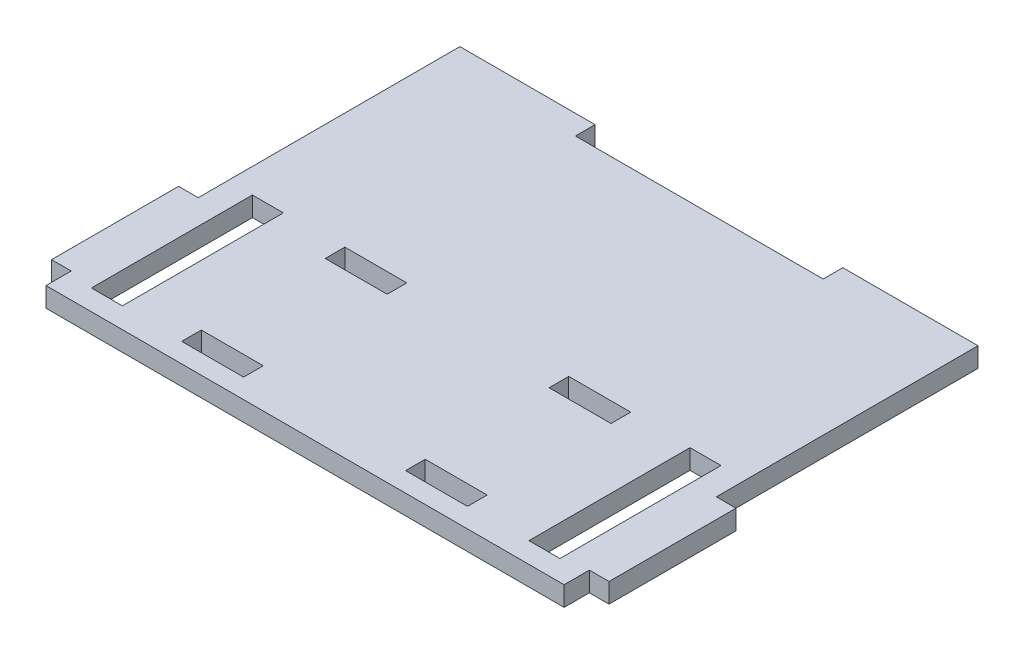
SolidWorks part; units mm, degrees
ref_plane "Front Plane" through (0, 0, 0) normal (0, 0, 1) x (1, 0, 0)
ref_plane "Top Plane" through (0, 0, 0) normal (0, 1, 0) x (1, 0, 0)
ref_plane "Right Plane" through (0, 0, 0) normal (1, 0, 0) x (0, 0, -1)
sketch "Sketch1" plane through (0, 0, 0) normal (0, 1, 0) x (1, 0, 0)
  line L0 (-41.825, 31.825) -> (41.825, 31.825)
  line L1 (-45, -35) -> (45, -35)
  line L2 (-45, -35) -> (-45, 35)
  line L3 (-45, 35) -> (45, 35)
  line L4 (45, -35) -> (45, 35)
  line L5 (-45, -35) -> (45, 35) construction
  line L6 (-45, 35) -> (45, -35) construction
  line L7 (41.825, -35) -> (41.825, 35)
  line L8 (-41.825, -31.825) -> (41.825, -31.825)
  line L9 (-41.825, -35) -> (-41.825, 35)
  line L10 (-41.825, -31.825) -> (-41.825, 31.825) construction
  line L11 (-20, 38.175) -> (20, 38.175)
  line L12 (-20, 38.175) -> (-20, 31.825)
  line L13 (-20, 31.825) -> (20, 31.825)
  line L14 (20, 38.175) -> (20, 31.825)
  line L15 (-20, 38.175) -> (20, 31.825) construction
  line L16 (-20, 31.825) -> (20, 38.175) construction
  line L17 (-20, -38.175) -> (20, -38.175)
  line L18 (-20, -38.175) -> (-20, -31.825)
  line L19 (-20, -31.825) -> (20, -31.825)
  line L20 (20, -38.175) -> (20, -31.825)
  line L21 (-20, -38.175) -> (20, -31.825) construction
  line L22 (-20, -31.825) -> (20, -38.175) construction
  line L23 (-48.175, -27.75) -> (-41.825, -27.75)
  line L24 (-48.175, -27.75) -> (-48.175, -7.25)
  line L25 (-48.175, -7.25) -> (-41.825, -7.25)
  line L26 (-41.825, -27.75) -> (-41.825, -7.25)
  line L27 (-48.175, -27.75) -> (-41.825, -7.25) construction
  line L28 (-48.175, -7.25) -> (-41.825, -27.75) construction
  line L29 (0, 0) -> (0, -35) construction
  line L30 (48.175, -7.25) -> (41.825, -27.75) construction
  line L31 (48.175, -27.75) -> (41.825, -7.25) construction
  line L32 (41.825, -27.75) -> (41.825, -7.25)
  line L33 (48.175, -7.25) -> (41.825, -7.25)
  line L34 (48.175, -27.75) -> (48.175, -7.25)
  line L35 (41.825, -31.825) -> (41.825, 31.825) construction
  line L36 (48.175, -27.75) -> (41.825, -27.75)
  point P0 (0, 0)
  point P10 (0, 35)
  point P15 (0, -35)
  point P20 (-45, 0)
  point P35 (45, -17.5)
  point P36 (-45, -17.5)
  dimension "D1" = 70
  dimension "D2" = 90
  dimension "D4" = 40
  dimension "D5" = 20.5
  dimension "D6" = 17.5
  dimension "D3" = 3.175
extrude "Boss-Extrude1" add sketch "Sketch1" along normal blind 3.175 contours L9 L8 L7 L0 | L3 L14 L0 L7 | L12 L3 L9 L0 | L25 L2 L23 L9 | L36 L4 L33 L7
sketch "Sketch2" plane through (0, 3.175, 0) normal (0, 1, 0) x (1, 0, 0)
  line L1 (-37.825, -28.5) -> (-32.825, -28.5)
  line L2 (-37.825, -28.5) -> (-37.825, -2.5)
  line L3 (-37.825, -2.5) -> (-32.825, -2.5)
  line L4 (-32.825, -28.5) -> (-32.825, -2.5)
  line L5 (-37.825, -28.5) -> (-32.825, -2.5) construction
  line L6 (-37.825, -2.5) -> (-32.825, -28.5) construction
  line L7 (-41.825, -31.825) -> (-41.825, -27.75) construction
  line L8 (0, -31.825) -> (0, 31.825) construction
  line L9 (-41.825, -31.825) -> (41.825, -31.825) construction
  line L10 (-20, 31.825) -> (20, 31.825) construction
  line L11 (37.825, -2.5) -> (32.825, -28.5) construction
  line L12 (37.825, -28.5) -> (32.825, -2.5) construction
  line L13 (32.825, -28.5) -> (32.825, -2.5)
  line L14 (37.825, -2.5) -> (32.825, -2.5)
  line L15 (37.825, -28.5) -> (37.825, -2.5)
  line L16 (37.825, -28.5) -> (32.825, -28.5)
  line L17 (-35.325, -15.5) -> (35.325, -15.5) construction
  line L18 (-18.075, -15.5) -> (-18.075, -3.9125) construction
  line L19 (23.075, -2.325) -> (13.075, -5.5) construction
  line L20 (-23.075, -5.5) -> (-13.075, -5.5)
  line L21 (-23.075, -5.5) -> (-23.075, -2.325)
  line L22 (-23.075, -2.325) -> (-13.075, -2.325)
  line L23 (-13.075, -5.5) -> (-13.075, -2.325)
  line L24 (-23.075, -5.5) -> (-13.075, -2.325) construction
  line L25 (-23.075, -2.325) -> (-13.075, -5.5) construction
  line L26 (23.075, -5.5) -> (13.075, -2.325) construction
  line L27 (13.075, -5.5) -> (13.075, -2.325)
  line L28 (23.075, -2.325) -> (13.075, -2.325)
  line L29 (23.075, -5.5) -> (23.075, -2.325)
  line L30 (23.075, -5.5) -> (13.075, -5.5)
  line L31 (23.075, -25.5) -> (13.075, -28.675) construction
  line L32 (23.075, -28.675) -> (13.075, -25.5) construction
  line L33 (23.075, -25.5) -> (13.075, -25.5)
  line L34 (23.075, -25.5) -> (23.075, -28.675)
  line L35 (23.075, -28.675) -> (13.075, -28.675)
  line L36 (13.075, -25.5) -> (13.075, -28.675)
  line L37 (-23.075, -28.675) -> (-13.075, -25.5) construction
  line L38 (-23.075, -25.5) -> (-13.075, -28.675) construction
  line L39 (-13.075, -25.5) -> (-13.075, -28.675)
  line L40 (-23.075, -28.675) -> (-13.075, -28.675)
  line L41 (-23.075, -25.5) -> (-23.075, -28.675)
  line L42 (-23.075, -25.5) -> (-13.075, -25.5)
  line L45 (-41.825, -35) -> (41.825, -35)
  line L46 (-41.825, -35) -> (41.825, -35) construction
  point P0 (-35.325, -15.5)
  point P19 (35.325, -15.5)
  dimension "D1" = 26
  dimension "D2" = 19.5
  dimension "D3" = 5
  dimension "D4" = 4
  dimension "D5" = 11.5875
  dimension "D6" = 3.175
  dimension "D7" = 10
  dimension "D8" = 9.75
  dimension "D9" = 3.175
extrude "Cut-Extrude1" cut sketch "Sketch2" against normal blind 23.175
